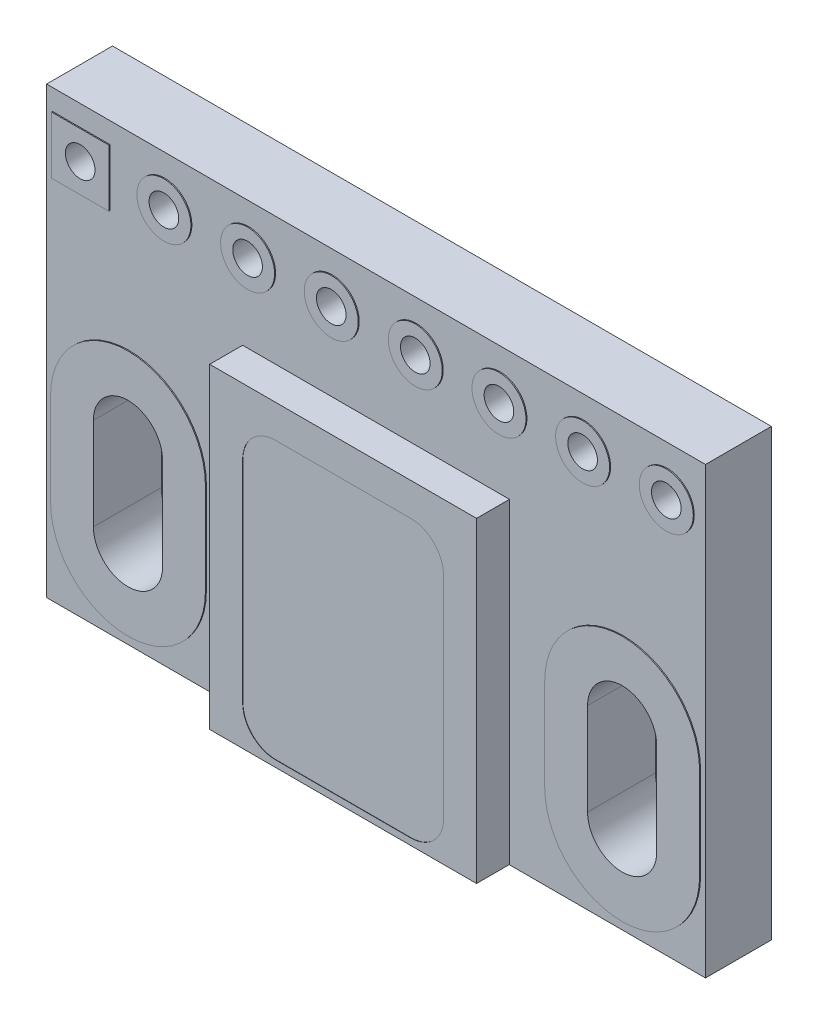
SolidWorks part; units mm, degrees
ref_plane "Front Plane" through (0, 0, 0) normal (0, 0, 1) x (1, 0, 0)
ref_plane "Top Plane" through (0, 0, 0) normal (0, 1, 0) x (1, 0, 0)
ref_plane "Right Plane" through (0, 0, 0) normal (1, 0, 0) x (0, 0, -1)
sketch "Sketch1" plane through (0, 0, 0) normal (0, 0, 1) x (1, 0, 0)
  line L0 (238.5, 243.4) -> (238.5, 240.6) construction
  line L1 (236, 251.5) -> (256, 251.5)
  line L2 (236, 251.5) -> (236, 238)
  line L3 (236, 238) -> (256, 238)
  line L4 (256, 251.5) -> (256, 238)
  line L5 (239.55, 243.4) -> (239.55, 240.6)
  line L6 (237.45, 243.4) -> (237.45, 240.6)
  line L7 (253.5, 243.4) -> (253.5, 240.6) construction
  line L8 (254.55, 243.4) -> (254.55, 240.6)
  line L9 (252.45, 243.4) -> (252.45, 240.6)
  circle A0 centre (237.05, 250) radius 0.45
  circle A1 centre (239.59, 250) radius 0.45
  circle A2 centre (242.13, 250) radius 0.45
  circle A3 centre (244.67, 250) radius 0.45
  circle A4 centre (247.22, 250) radius 0.45
  circle A5 centre (249.76, 250) radius 0.45
  circle A6 centre (252.3, 250) radius 0.45
  circle A7 centre (254.84, 250) radius 0.45
  arc A8 (239.55, 243.4) -> (237.45, 243.4) centre (238.5, 243.4) ccw
  arc A9 (237.45, 240.6) -> (239.55, 240.6) centre (238.5, 240.6) ccw
  arc A10 (254.55, 243.4) -> (252.45, 243.4) centre (253.5, 243.4) ccw
  arc A11 (252.45, 240.6) -> (254.55, 240.6) centre (253.5, 240.6) ccw
  point P25 (238.5, 242)
  point P30 (253.5, 242)
  dimension "D1" = 2.1
  dimension "D2" = 2.1
extrude "Boss-Extrude1" add sketch "Sketch1" along normal blind 2
sketch "Sketch2" plane through (0, 0, 2) normal (0, 0, 1) x (1, 0, 0)
  line L1 (237.9195, 250.8695) -> (236.1805, 250.8695)
  line L2 (236.1805, 250.8695) -> (236.1805, 249.1305)
  line L3 (236.1805, 249.1305) -> (237.9195, 249.1305)
  line L4 (237.9195, 249.1305) -> (237.9195, 250.8695)
  line L10 (239.55, 240.6) -> (239.55, 243.4)
  line L11 (237.45, 243.4) -> (237.45, 240.6)
  line L12 (239.55, 240.6) -> (239.55, 243.4)
  line L13 (237.45, 243.4) -> (237.45, 240.6)
  line L16 (240.85, 240.6) -> (240.85, 243.4)
  line L17 (236.15, 243.4) -> (236.15, 240.6)
  line L18 (254.55, 240.6) -> (254.55, 243.4)
  line L19 (252.45, 243.4) -> (252.45, 240.6)
  line L20 (254.55, 240.6) -> (254.55, 243.4)
  line L21 (252.45, 243.4) -> (252.45, 240.6)
  line L22 (255.85, 240.6) -> (255.85, 243.4)
  line L23 (251.15, 243.4) -> (251.15, 240.6)
  circle A0 centre (237.05, 250) radius 0.45
  circle A1 centre (239.59, 250) radius 0.45
  circle A2 centre (242.13, 250) radius 0.45
  circle A3 centre (244.67, 250) radius 0.45
  circle A4 centre (247.22, 250) radius 0.45
  circle A5 centre (249.76, 250) radius 0.45
  circle A6 centre (252.3, 250) radius 0.45
  circle A7 centre (254.84, 250) radius 0.45
  circle A8 centre (254.84, 250) radius 0.8196
  circle A9 centre (252.3, 250) radius 0.8196
  circle A10 centre (249.76, 250) radius 0.8196
  circle A11 centre (247.22, 250) radius 0.8196
  circle A12 centre (244.67, 250) radius 0.8196
  circle A13 centre (242.13, 250) radius 0.8196
  circle A14 centre (239.59, 250) radius 0.8196
  circle A15 centre (237.05, 250) radius 0.8695 construction
  arc A24 (239.55, 243.4) -> (237.45, 243.4) centre (238.5, 243.4) ccw
  arc A25 (237.45, 240.6) -> (239.55, 240.6) centre (238.5, 240.6) ccw
  arc A26 (239.55, 243.4) -> (237.45, 243.4) centre (238.5, 243.4) ccw
  arc A27 (237.45, 240.6) -> (239.55, 240.6) centre (238.5, 240.6) ccw
  arc A32 (240.85, 243.4) -> (236.15, 243.4) centre (238.5, 243.4) ccw
  arc A33 (236.15, 240.6) -> (240.85, 240.6) centre (238.5, 240.6) ccw
  arc A34 (254.55, 243.4) -> (252.45, 243.4) centre (253.5, 243.4) ccw
  arc A35 (252.45, 240.6) -> (254.55, 240.6) centre (253.5, 240.6) ccw
  arc A36 (254.55, 243.4) -> (252.45, 243.4) centre (253.5, 243.4) ccw
  arc A37 (252.45, 240.6) -> (254.55, 240.6) centre (253.5, 240.6) ccw
  arc A38 (255.85, 243.4) -> (251.15, 243.4) centre (253.5, 243.4) ccw
  arc A39 (251.15, 240.6) -> (255.85, 240.6) centre (253.5, 240.6) ccw
  dimension "D1" = 0
  dimension "D2" = 0
  dimension "D3" = 1.3
extrude "Boss-Extrude2" add sketch "Sketch2" along normal blind 0.03 and the other way offset from surface (2.03 mm away) 0.03 other way up to face at (238.5, 242, 0)
sketch "Sketch3" plane through (0, 0, 2) normal (0, 0, 1) x (1, 0, 0)
  line L0 (241.95, 238.0083) -> (250.05, 238.0083)
  line L5 (241.95, 238.0083) -> (241.95, 247.6083)
  line L6 (241.95, 247.6083) -> (250.05, 247.6083)
  line L7 (250.05, 238.0083) -> (250.05, 247.6083)
  line L8 (240.85, 240.6) -> (240.85, 243.4) construction
  line L9 (251.15, 243.4) -> (251.15, 240.6) construction
  dimension "D1" = 1.1
  dimension "D2" = 1.1
  dimension "D3" = 9.6
extrude "Boss-Extrude3" add sketch "Sketch3" along normal blind 1
sketch "Sketch4" plane through (0, 0, 0) normal (0, 0, -1) x (-1, 0, 0)
  line L0 (-244.4451, 243.8462) -> (-248.4451, 243.8462)
  line L5 (-244.4451, 243.8462) -> (-244.4451, 247.8462)
  line L6 (-244.4451, 247.8462) -> (-248.4451, 247.8462)
  line L7 (-248.4451, 243.8462) -> (-248.4451, 247.8462)
extrude "Boss-Extrude4" add sketch "Sketch4" along normal blind 0.9
sketch "Sketch5" plane through (0, 0, 0) normal (0, 0, -1) x (-1, 0, 0)
  line L0 (-250.05, 238.0083) -> (-250.05, 247.6083) construction
  line L1 (-241.95, 238.0083) -> (-250.05, 238.0083)
  line L2 (-241.95, 238.0083) -> (-241.95, 242.8083)
  line L3 (-241.95, 242.8083) -> (-250.05, 242.8083)
  line L4 (-250.05, 238.0083) -> (-250.05, 242.8083)
extrude "Boss-Extrude5" add sketch "Sketch5" along normal blind 1
sketch "Sketch6" plane through (0, 0, -1) normal (0, 0, -1) x (-1, 0, 0)
  line L0 (-241.95, 238.0083) -> (-241.95, 242.8083) construction
  line L1 (-243.95, 238.2083) -> (-248.05, 238.2083)
  line L2 (-242.95, 239.2083) -> (-242.95, 240.8083)
  line L3 (-243.95, 241.8083) -> (-248.05, 241.8083)
  line L4 (-249.05, 239.2083) -> (-249.05, 240.8083)
  line L5 (-241.95, 242.8083) -> (-250.05, 242.8083) construction
  line L6 (-250.05, 242.8083) -> (-250.05, 238.0083) construction
  line L7 (-250.05, 238.0083) -> (-241.95, 238.0083) construction
  arc A0 (-248.05, 238.2083) -> (-249.05, 239.2083) centre (-248.05, 239.2083) cw
  arc A1 (-242.95, 240.8083) -> (-243.95, 241.8083) centre (-243.95, 240.8083) ccw
  arc A2 (-248.05, 241.8083) -> (-249.05, 240.8083) centre (-248.05, 240.8083) ccw
  arc A3 (-243.95, 238.2083) -> (-242.95, 239.2083) centre (-243.95, 239.2083) ccw
  dimension "D5" = 1
  dimension "D1" = 1
  dimension "D2" = 1
  dimension "D3" = 1
  dimension "D4" = 0.2
extrude "Cut-Extrude1" cut sketch "Sketch6" against normal blind 0.01
sketch "Sketch7" plane through (0, 0, 3) normal (0, 0, 1) x (1, 0, 0)
  line L0 (250.05, 238.0083) -> (250.05, 247.6083) construction
  line L1 (248.05, 238.2083) -> (243.95, 238.2083)
  line L2 (249.05, 239.2083) -> (249.05, 245.6083)
  line L3 (248.05, 246.6083) -> (243.95, 246.6083)
  line L4 (242.95, 239.2083) -> (242.95, 245.6083)
  line L5 (241.95, 247.6083) -> (241.95, 238.0083) construction
  line L6 (250.05, 247.6083) -> (241.95, 247.6083) construction
  line L7 (241.95, 238.0083) -> (250.05, 238.0083) construction
  arc A0 (243.95, 238.2083) -> (242.95, 239.2083) centre (243.95, 239.2083) cw
  arc A1 (249.05, 245.6083) -> (248.05, 246.6083) centre (248.05, 245.6083) ccw
  arc A2 (243.95, 246.6083) -> (242.95, 245.6083) centre (243.95, 245.6083) ccw
  arc A3 (248.05, 238.2083) -> (249.05, 239.2083) centre (248.05, 239.2083) ccw
  dimension "D5" = 1
  dimension "D1" = 1
  dimension "D2" = 1
  dimension "D3" = 1
  dimension "D4" = 0.2
extrude "Cut-Extrude2" cut sketch "Sketch7" against normal blind 0.01
sketch "Sketch8" plane through (0, 0, 0) normal (0, 0, -1) x (-1, 0, 0)
  line L0 (-236.656, 248.1146) -> (-237.6556, 248.1146)
  line L9 (-236.656, 248.1146) -> (-236.656, 247.1249)
  line L10 (-236.656, 247.1249) -> (-237.6556, 247.1249)
  line L11 (-237.6556, 248.1146) -> (-237.6556, 247.1249)
  line L12 (-238.1032, 247.1249) -> (-239.1151, 247.1249)
  line L13 (-238.1032, 247.1249) -> (-238.1032, 248.1146)
  line L14 (-238.1032, 248.1146) -> (-239.1151, 248.1146)
  line L15 (-239.1151, 247.1249) -> (-239.1151, 248.1146)
extrude "Boss-Extrude6" add sketch "Sketch8" along normal up to surface (0.03 mm away) up to face at (238.5, 242, -0.03)
sketch "Sketch9" plane through (0, 0, 0) normal (0, 0, -1) x (-1, 0, 0)
  line L1 (-241.2857, 245.5798) -> (-242.3455, 245.5798)
  line L2 (-241.2857, 246.8313) -> (-241.7017, 246.8313)
  line L3 (-241.9386, 246.8313) -> (-242.3455, 246.8313)
  line L4 (-242.5857, 246.8313) -> (-242.8193, 246.8313)
  line L5 (-242.5857, 245.5798) -> (-242.8193, 245.5798)
  line L17 (-240.8056, 246.8313) -> (-241.0528, 246.8313)
  line L26 (-240.8056, 246.8313) -> (-240.8056, 245.5798)
  line L27 (-240.8056, 245.5798) -> (-241.0528, 245.5798)
  line L28 (-242.8193, 246.8313) -> (-242.8193, 245.5798)
  line L30 (-241.0528, 245.5798) -> (-241.0528, 245.1605)
  line L31 (-241.0528, 245.1605) -> (-241.2857, 245.1605)
  line L32 (-241.2857, 245.5798) -> (-241.2857, 245.1605)
  line L34 (-242.3455, 245.5798) -> (-242.3455, 245.1605)
  line L35 (-242.3455, 245.1605) -> (-242.5857, 245.1605)
  line L36 (-242.5857, 245.5798) -> (-242.5857, 245.1605)
  line L37 (-241.0528, 247.2948) -> (-241.2857, 247.2948)
  line L38 (-241.0528, 247.2948) -> (-241.0528, 246.8313)
  line L40 (-241.2857, 247.2948) -> (-241.2857, 246.8313)
  line L41 (-241.7017, 247.2948) -> (-241.9386, 247.2948)
  line L42 (-241.7017, 247.2948) -> (-241.7017, 246.8313)
  line L44 (-241.9386, 247.2948) -> (-241.9386, 246.8313)
  line L45 (-242.3455, 247.2948) -> (-242.5857, 247.2948)
  line L46 (-242.3455, 247.2948) -> (-242.3455, 246.8313)
  line L48 (-242.5857, 247.2948) -> (-242.5857, 246.8313)
extrude "Boss-Extrude7" add sketch "Sketch9" along normal blind 1
sketch "Sketch10" plane through (240.8056, 0, 0) normal (-1, 0, 0) x (0, 0, 1)
  line L0 (-1, 246.8313) -> (0, 246.8313) construction
  line L1 (-1, 246.8313) -> (0, 246.8313) construction
  line L2 (-0.1399, 247.2611) -> (-0.1399, 247.6543)
  line L3 (-1, 245.5798) -> (0, 245.5798) construction
  line L4 (0, 251.5) -> (0, 238) construction
  line L5 (0, 245.75) -> (0, 243.4) construction
  line L6 (-0.03, 245.75) -> (-0.03, 243.4) construction
  line L17 (-0.1399, 247.6543) -> (-1.1393, 247.6306)
  line L19 (-0.1688, 244.7145) -> (-1.19, 244.7145)
  line L29 (0, 247.138) -> (0, 245.2719)
  line L30 (-0.1229, 245.5946) -> (-0.5513, 245.5798)
  line L31 (-0.5513, 245.5798) -> (-0.5513, 245.5128)
  line L32 (-0.5513, 245.5128) -> (-0.5259, 245.4665)
  line L33 (-0.5259, 245.4665) -> (-0.4802, 245.4523)
  line L34 (-0.4802, 245.4523) -> (-0.1926, 245.4523)
  line L35 (-0.1926, 245.4523) -> (-0.1359, 245.4347)
  line L36 (-0.1359, 245.4347) -> (-0.0802, 245.3984)
  line L37 (-0.0802, 245.3984) -> (-0.03, 245.334)
  line L38 (-0.03, 245.334) -> (-0.0186, 245.3133)
  line L39 (-0.0186, 245.3133) -> (0, 245.2719)
  line L40 (-0.1688, 244.7145) -> (-0.1688, 245.2473)
  line L41 (-0.1688, 245.2473) -> (-0.1949, 245.2949)
  line L42 (-0.1949, 245.2949) -> (-0.2419, 245.3095)
  line L43 (-0.2419, 245.3095) -> (-0.4281, 245.3095)
  line L44 (-0.4281, 245.3095) -> (-0.5376, 245.3124)
  line L45 (-0.5376, 245.3124) -> (-0.633, 245.3623)
  line L46 (-0.633, 245.3623) -> (-0.6884, 245.4634)
  line L47 (-0.6884, 245.4634) -> (-0.6925, 245.5798)
  line L48 (-0.1399, 247.2611) -> (-0.1399, 247.1761)
  line L58 (-0.1399, 247.1761) -> (-0.1751, 247.1126)
  line L59 (-0.1751, 247.1126) -> (-0.2149, 247.1011)
  line L71 (-0.2149, 247.1011) -> (-0.4649, 247.1011)
  line L72 (-0.4649, 247.1011) -> (-0.571, 247.0707)
  line L73 (-0.571, 247.0707) -> (-0.6177, 247.0302)
  line L74 (-0.6177, 247.0302) -> (-0.6595, 246.9473)
  line L75 (-0.6595, 246.9473) -> (-0.6649, 246.8313)
  line L76 (-0.6649, 246.8313) -> (-1.1393, 246.7681)
  line L77 (0, 247.138) -> (-0.0199, 247.0616)
  line L78 (-0.0199, 247.0616) -> (-0.0585, 247.0149)
  line L79 (-0.0585, 247.0149) -> (-0.1229, 246.9718)
  line L80 (-0.1229, 246.9718) -> (-0.1999, 246.9563)
  line L81 (-0.1999, 246.9563) -> (-0.4499, 246.9563)
  line L82 (-0.4499, 246.9563) -> (-0.4904, 246.9444)
  line L83 (-0.4904, 246.9444) -> (-0.5184, 246.912)
  line L84 (-0.5184, 246.912) -> (-0.5249, 246.8813)
  line L85 (-0.5249, 246.8813) -> (-0.5249, 246.8313)
  line L86 (-0.5249, 246.8313) -> (-0.1229, 246.8207)
  line L87 (-0.1229, 246.8207) -> (-0.1229, 245.5946)
  line L88 (-0.6925, 245.5798) -> (-1.19, 245.5935)
  line L89 (-1.1393, 246.7681) -> (-1.1393, 247.6306)
  line L90 (-1.19, 245.5935) -> (-1.19, 244.7145)
extrude "Cut-Extrude3" cut sketch "Sketch10" against normal blind 2.6
sketch "Sketch11" plane through (0, 0, 0) normal (0, 0, -1) x (-1, 0, 0)
  line L10 (-249.6266, 246.1593) -> (-250.1597, 246.1593)
  line L11 (-249.6266, 246.1593) -> (-249.6266, 247.2032)
  line L12 (-249.6266, 247.2032) -> (-250.1597, 247.2032)
  line L13 (-250.1597, 246.1593) -> (-250.1597, 247.2032)
  line L14 (-250.7028, 246.2088) -> (-251.2294, 246.2088)
  line L15 (-250.7028, 246.2088) -> (-250.7028, 247.2632)
  line L16 (-250.7028, 247.2632) -> (-251.2294, 247.2632)
  line L17 (-251.2294, 246.2088) -> (-251.2294, 247.2632)
extrude "Boss-Extrude8" add sketch "Sketch11" along normal blind 0.5
sketch "Sketch12" plane through (0, 0, -0.5) normal (0, 0, -1) x (-1, 0, 0)
  line L1 (-249.5049, 246.4062) -> (-250.2952, 246.4062)
  line L2 (-249.5049, 246.4062) -> (-249.5049, 246.9346)
  line L3 (-249.5049, 246.9346) -> (-250.2952, 246.9346)
  line L4 (-250.2952, 246.4062) -> (-250.2952, 246.9346)
  line L5 (-250.5662, 246.4521) -> (-251.3473, 246.4521)
  line L6 (-250.5662, 246.4521) -> (-250.5662, 247.0402)
  line L7 (-250.5662, 247.0402) -> (-251.3473, 247.0402)
  line L8 (-251.3473, 246.4521) -> (-251.3473, 247.0402)
extrude "Cut-Extrude4" cut sketch "Sketch12" against normal blind 0.01
